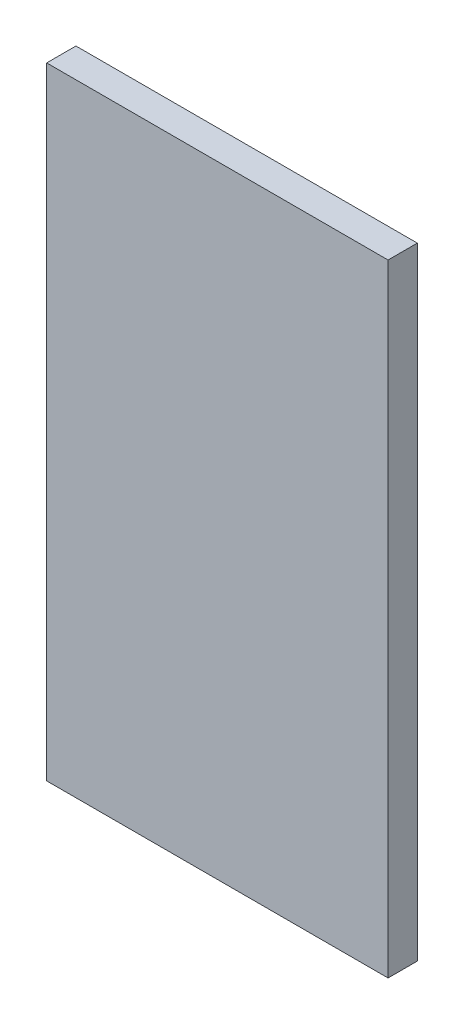
SolidWorks part; units mm, degrees
ref_plane "Front Plane" through (0, 0, 0) normal (0, 0, 1) x (1, 0, 0)
ref_plane "Top Plane" through (0, 0, 0) normal (0, 1, 0) x (1, 0, 0)
ref_plane "Right Plane" through (0, 0, 0) normal (1, 0, 0) x (0, 0, -1)
sketch "Sketch2" plane through (0, 0, 0) normal (0, 0, 1) x (1, 0, 0)
  line L1 (35, -63.75) -> (-35, -63.75)
  line L2 (35, -63.75) -> (35, 63.75)
  line L3 (35, 63.75) -> (-35, 63.75)
  line L4 (-35, -63.75) -> (-35, 63.75)
  line L5 (35, -63.75) -> (-35, 63.75) construction
  line L6 (35, 63.75) -> (-35, -63.75) construction
  point P0 (0, 0)
  dimension "D1" = 70
  dimension "D2" = 127.5
extrude "Boss-Extrude1" add sketch "Sketch2" along normal blind 6
